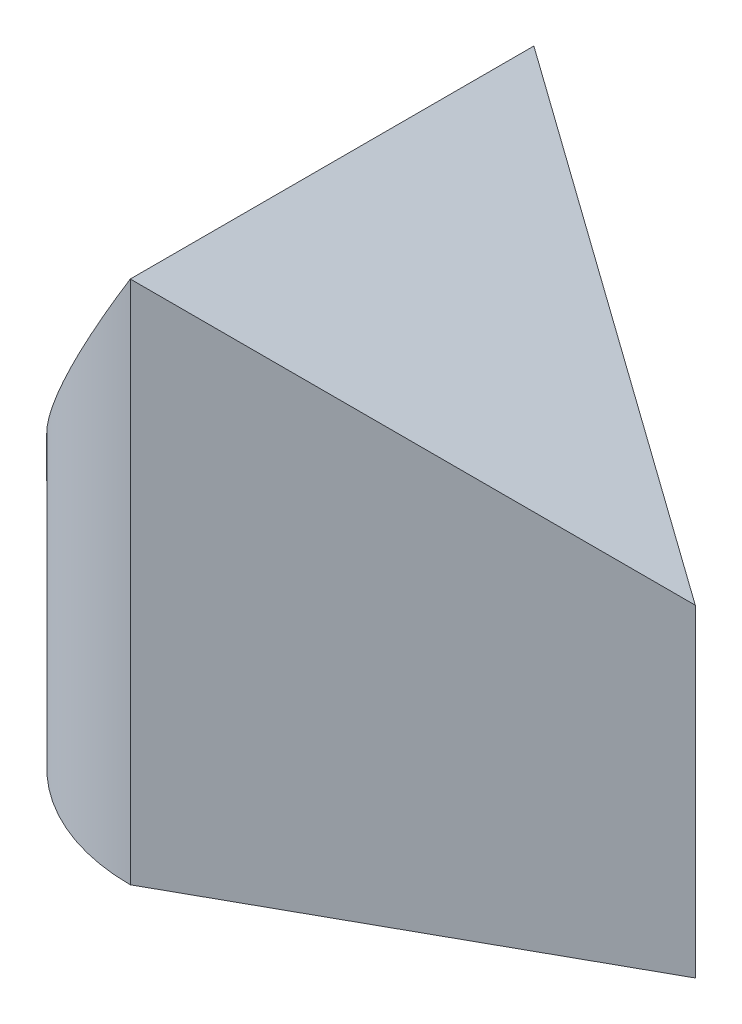
SolidWorks part; units mm, degrees
ref_plane "Front" through (0, 0, 0) normal (0, 0, 1) x (1, 0, 0)
ref_plane "Top" through (0, 0, 0) normal (0, 1, 0) x (1, 0, 0)
ref_plane "Right" through (0, 0, 0) normal (1, 0, 0) x (0, 0, -1)
sketch "Sketch1" plane through (0, 0, 0) normal (0, 1, 0) x (1, 0, 0)
  line L2 (0, 25) -> (45, 0)
  line L3 (45, 0) -> (0, -25)
  arc A0 (0, 25) -> (0, -25) centre (0, 0) ccw
extrude "Extrude1" add sketch "Sketch1" along normal blind 65
sketch "Sketch2" plane through (0, 0, 0) normal (0, 0, 1) x (1, 0, 0)
  line L0 (0, 65) -> (45, 65)
  line L1 (45, 65) -> (45, 40)
  line L2 (45, 65) -> (45, 0) construction
  line L3 (45, 40) -> (0, 65)
  line L4 (0, 65) -> (-25, 65)
  line L5 (-25, 65) -> (-25, 24)
  line L6 (-25, 24) -> (0, 65)
  dimension "D1" = 25
  dimension "D2" = 41
extrude "Cut-Extrude1" cut sketch "Sketch2" against normal mid plane 50 contours L0 L1 L3 | L4 L5 L6
